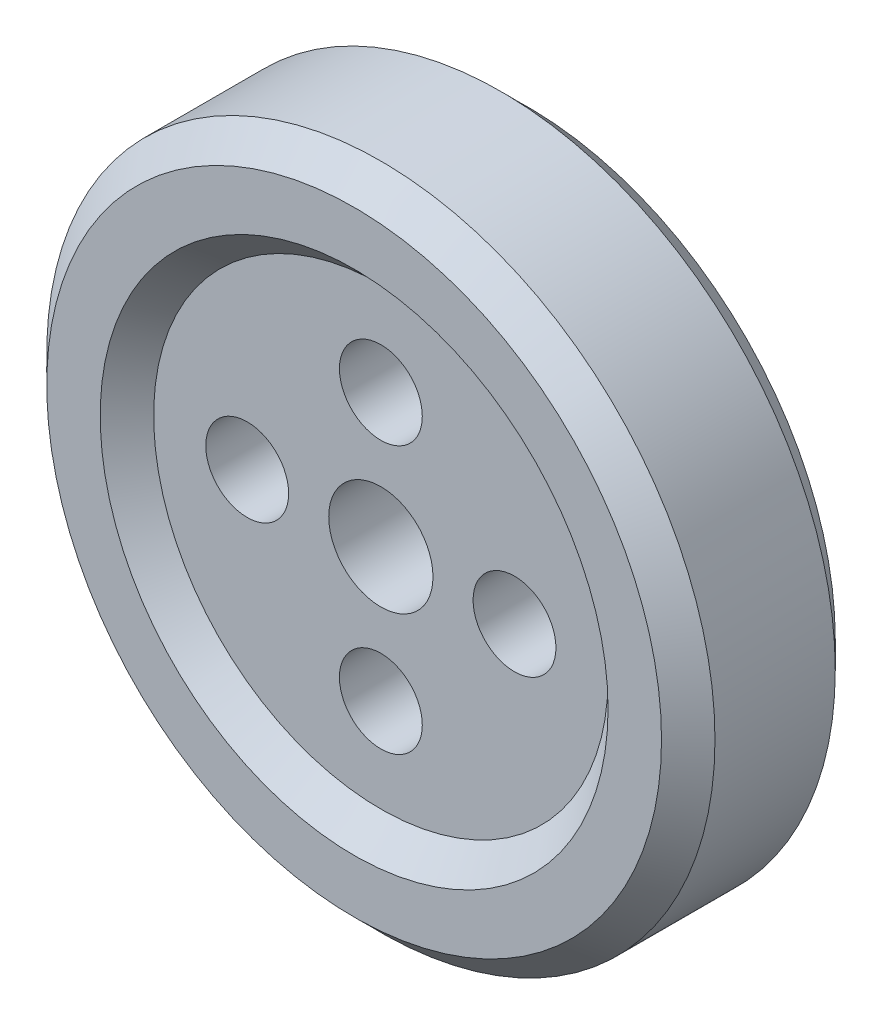
SolidWorks part; units mm, degrees
ref_plane "Front Plane" through (0, 0, 0) normal (0, 0, 1) x (1, 0, 0)
ref_plane "Top Plane" through (0, 0, 0) normal (0, 1, 0) x (1, 0, 0)
ref_plane "Right Plane" through (0, 0, 0) normal (1, 0, 0) x (0, 0, -1)
sketch "Sketch1" plane through (0, 0, 0) normal (0, 0, 1) x (1, 0, 0)
  circle A0 centre (0, 0) radius 250
  dimension "D1" = 500
extrude "Boss-Extrude1" add sketch "Sketch1" along normal mid plane 130
chamfer "Chamfer1" distance 20 angle 45 2 edges at (250, 0, -65) (250, 0, 65)
sketch "Sketch2" plane through (0, 0, 65) normal (0, 0, 1) x (1, 0, 0)
  circle A0 centre (0, 0) radius 190
  dimension "D1" = 380
extrude "Cut-Extrude1" cut sketch "Sketch2" against normal blind 20 draft 45
sketch "Sketch3" plane through (0, 0, -65) normal (0, 0, -1) x (-1, 0, 0)
  circle A0 centre (0, 0) radius 190
  dimension "D1" = 380
extrude "Cut-Extrude2" cut sketch "Sketch3" against normal blind 20 draft 45
sketch "Sketch4" plane through (0, 0, -45) normal (0, 0, -1) x (-1, 0, 0)
  circle A0 centre (0, 0) radius 100 construction
  circle A1 centre (0, 100) radius 31
  circle A2 centre (-100, 0) radius 31
  circle A3 centre (0, -100) radius 31
  circle A4 centre (100, 0) radius 31
  circle A5 centre (0, 0) radius 39
  dimension "D1" = 200
  dimension "D2" = 62
  dimension "D3" = 78
extrude "Cut-Extrude3" cut sketch "Sketch4" against normal through all
